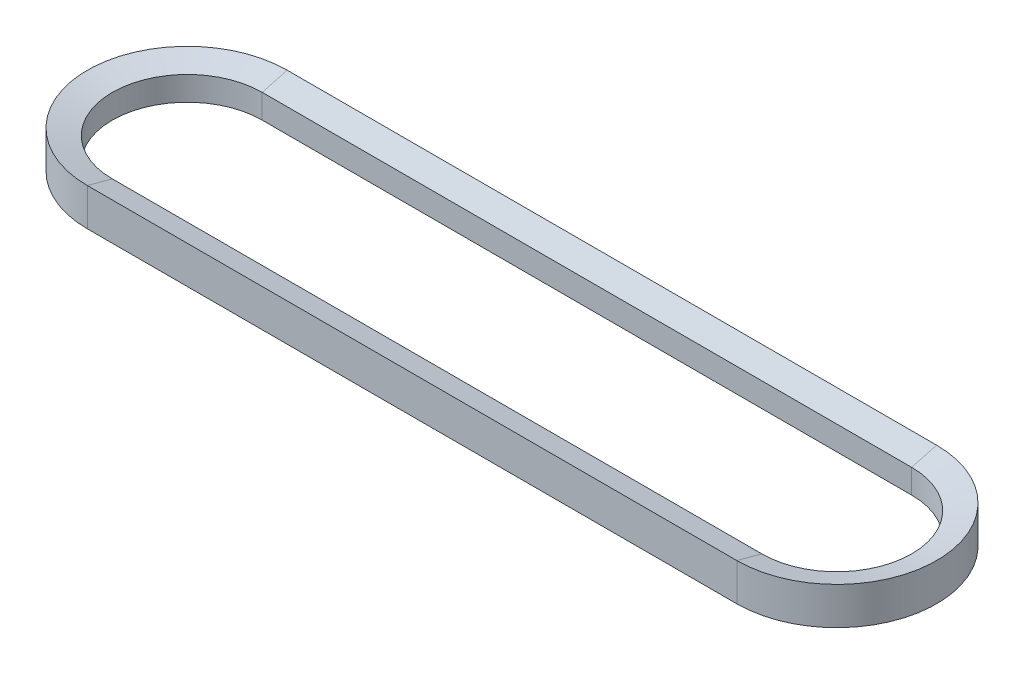
SolidWorks part; units mm, degrees
material "Rubber"
ref_plane "Front Plane" through (0, 0, 0) normal (0, 0, 1) x (1, 0, 0)
ref_plane "Top Plane" through (0, 0, 0) normal (0, 1, 0) x (1, 0, 0)
ref_plane "Right Plane" through (0, 0, 0) normal (1, 0, 0) x (0, 0, -1)
sketch "Sketch1" plane through (0, 0, 0) normal (0, 1, 0) x (1, 0, 0)
  line L0 (165.1, 0) -> (-165.1, 0) construction
  line L1 (165.1, -50.8) -> (-165.1, -50.8)
  line L2 (165.1, 50.8) -> (-165.1, 50.8)
  arc A0 (165.1, -50.8) -> (165.1, 50.8) centre (165.1, 0) ccw
  arc A1 (-165.1, 50.8) -> (-165.1, -50.8) centre (-165.1, 0) ccw
  point P2 (0, 0)
  dimension "D1" = 101.6
  dimension "D2" = 330.2
ref_plane "Plane1" through (-165.1, 0, -50.8) normal (-1, 0, 0) x (0, 0, 1)
sketch "Sketch2" plane through (-165.1, 0, -50.8) normal (-1, 0, 0) x (0, 0, 1)
  line L0 (0, 0) -> (0, 9.525)
  line L1 (0, 0) -> (0, -9.525)
  line L2 (0, -9.525) -> (12.7, -6.122)
  line L3 (12.7, -6.122) -> (12.7, 6.122)
  line L4 (12.7, 6.122) -> (0, 9.525)
  dimension "D1" = 19.05
  dimension "D2" = 30
  dimension "D3" = 12.7
sweep "Sweep1" add profiles "Sketch2" path "Sketch1"
